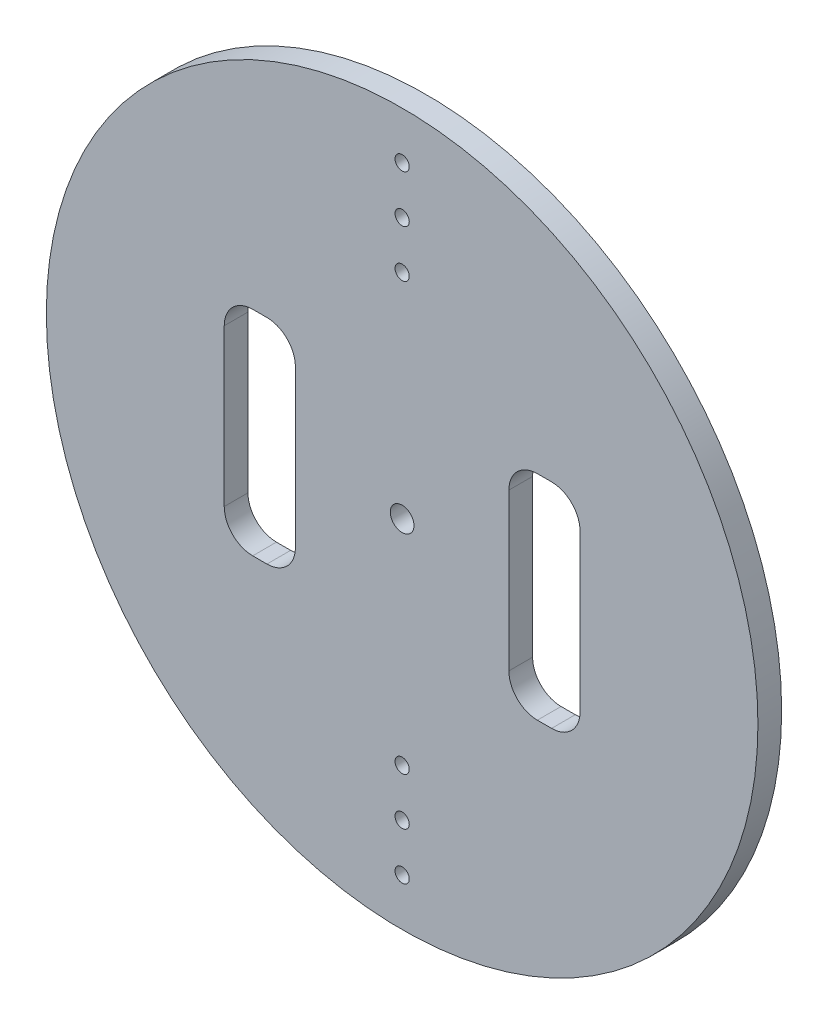
SolidWorks part; units mm, degrees
material "Acrílico (médio-alto impacto)"
ref_plane "Plano frontal" through (0, 0, 0) normal (0, 0, 1) x (1, 0, 0)
ref_plane "Plano superior" through (0, 0, 0) normal (0, 1, 0) x (1, 0, 0)
ref_plane "Plano direito" through (0, 0, 0) normal (1, 0, 0) x (0, 0, -1)
sketch "Esboço1" plane through (0, 0, 0) normal (0, 0, 1) x (1, 0, 0)
  circle A0 centre (0, 0) radius 75
  dimension "D1" = 150
extrude "Ressalto-extrusão1" add sketch "Esboço1" along normal blind 5
sketch "Esboço2" plane through (0, 0, 0) normal (0, 0, -1) x (-1, 0, 0)
  circle A0 centre (0, 0) radius 2.5
  dimension "D1" = 5
extrude "Corte-extrusão1" cut sketch "Esboço2" against normal blind 10
sketch "Esboço3" plane through (0, 0, 0) normal (0, 0, -1) x (-1, 0, 0)
  line L0 (0, 0) -> (0, -12.441) construction
  line L1 (0, 0) -> (17.6283, 0) construction
  circle A0 centre (0, -45) radius 1.5
  circle A1 centre (0, -55) radius 1.5
  circle A2 centre (0, -65) radius 1.5
  circle A3 centre (0, 0) radius 75 construction
  circle A4 centre (0, 65) radius 1.5
  circle A5 centre (0, 55) radius 1.5
  circle A6 centre (0, 45) radius 1.5
  dimension "D1" = 10
  dimension "D2" = 3
  dimension "D3" = 3
  dimension "D4" = 10
  dimension "D5" = 3
  dimension "D6" = 45
extrude "Corte-extrusão2" cut sketch "Esboço3" against normal blind 10
sketch "Esboço4" plane through (0, 0, 0) normal (0, 0, -1) x (-1, 0, 0)
  line L1 (-31.5, -22.5) -> (-28.5, -22.5)
  line L2 (-37.5, -16.5) -> (-37.5, 16.5)
  line L3 (-31.5, 22.5) -> (-28.5, 22.5)
  line L4 (-22.5, -16.5) -> (-22.5, 16.5)
  line L5 (28.5, -22.5) -> (31.5, -22.5)
  line L6 (22.5, -16.5) -> (22.5, 16.5)
  line L7 (28.5, 22.5) -> (31.5, 22.5)
  line L8 (37.5, -16.5) -> (37.5, 16.5)
  circle A1 centre (0, 0) radius 75 construction
  circle A2 centre (0, 0) radius 2.5 construction
  arc A3 (31.5, -22.5) -> (37.5, -16.5) centre (31.5, -16.5) ccw
  arc A4 (28.5, -22.5) -> (22.5, -16.5) centre (28.5, -16.5) cw
  arc A5 (31.5, 22.5) -> (37.5, 16.5) centre (31.5, 16.5) cw
  arc A6 (22.5, 16.5) -> (28.5, 22.5) centre (28.5, 16.5) cw
  arc A7 (-37.5, 16.5) -> (-31.5, 22.5) centre (-31.5, 16.5) cw
  arc A8 (-28.5, 22.5) -> (-22.5, 16.5) centre (-28.5, 16.5) cw
  arc A9 (-31.5, -22.5) -> (-37.5, -16.5) centre (-31.5, -16.5) cw
  arc A10 (-28.5, -22.5) -> (-22.5, -16.5) centre (-28.5, -16.5) ccw
  point P8 (30, 22.5)
  dimension "D11" = 6
  dimension "D1" = 45
  dimension "D2" = 45
  dimension "D3" = 22.5
  dimension "D4" = 22.5
  dimension "D5" = 22.5
  dimension "D6" = 22.5
  dimension "D7" = 15
  dimension "D8" = 15
  dimension "D9" = 37.5
  dimension "D10" = 37.5
extrude "Corte-extrusão3" cut sketch "Esboço4" against normal through all
